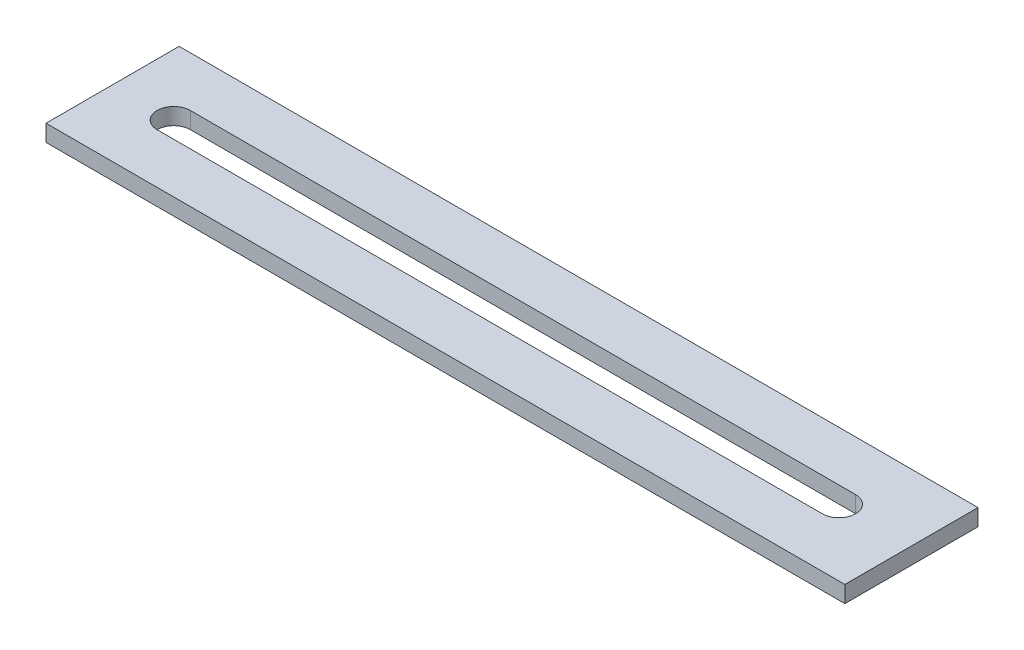
SolidWorks part; units mm, degrees
ref_plane "Front" through (0, 0, 0) normal (0, 0, 1) x (1, 0, 0)
ref_plane "Top" through (0, 0, 0) normal (0, 1, 0) x (1, 0, 0)
ref_plane "Right" through (0, 0, 0) normal (1, 0, 0) x (0, 0, -1)
sketch "Sketch1" plane through (0, 0, 0) normal (0, 1, 0) x (1, 0, 0)
  line L0 (11.6633, 12.7) -> (138.5768, 12.7) construction
  line L1 (0, 0) -> (152.4, 0)
  line L2 (0, 0) -> (0, 25.4)
  line L3 (0, 25.4) -> (152.4, 25.4)
  line L4 (152.4, 0) -> (152.4, 25.4)
  line L5 (11.6633, 15.875) -> (138.5768, 15.875)
  line L6 (11.6633, 9.525) -> (138.5768, 9.525)
  line L7 (0, 12.7) -> (8.4883, 12.7) construction
  arc A0 (11.6633, 15.875) -> (11.6633, 9.525) centre (11.6633, 12.7) ccw
  arc A1 (138.5768, 9.525) -> (138.5768, 15.875) centre (138.5768, 12.7) ccw
  point P5 (75.12, 12.7)
  dimension "D1" = 25.4
  dimension "D2" = 152.4
extrude "Boss-Extrude1" add sketch "Sketch1" along normal blind 3.175
